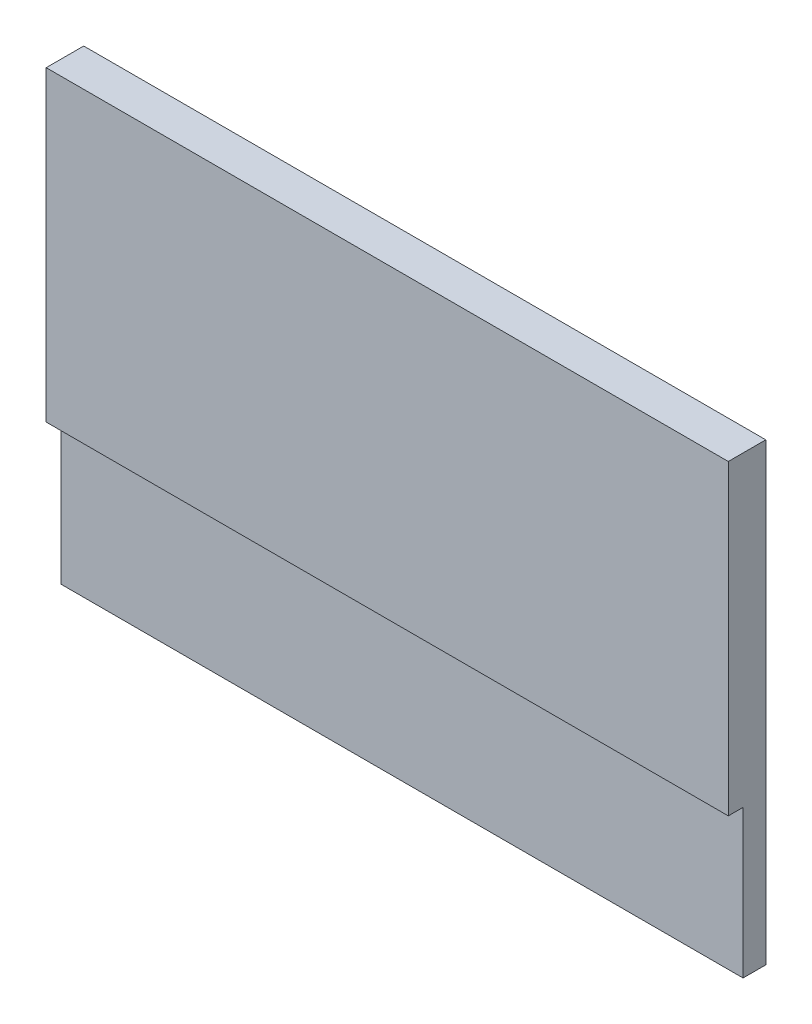
SolidWorks part; units mm, degrees
ref_plane "正面" through (0, 0, 0) normal (0, 0, 1) x (1, 0, 0)
ref_plane "平面" through (0, 0, 0) normal (0, 1, 0) x (1, 0, 0)
ref_plane "右側面" through (0, 0, 0) normal (1, 0, 0) x (0, 0, -1)
sketch "ｽｹｯﾁ1" plane through (0, 0, 0) normal (0, 0, 1) x (1, 0, 0)
  line L1 (0, 0) -> (30, 0)
  line L2 (0, 0) -> (0, 20)
  line L3 (0, 20) -> (30, 20)
  line L4 (30, 0) -> (30, 20)
  dimension "D1" = 30
  dimension "D2" = 20
extrude "ﾎﾞｽ - 押し出し1" add sketch "ｽｹｯﾁ1" along normal blind 1.65
sketch "ｽｹｯﾁ2" plane through (0, 0, 1.65) normal (0, 0, 1) x (1, 0, 0)
  line L0 (30, 0) -> (30, 20) construction
  line L1 (0, 0) -> (30, 0)
  line L2 (0, 0) -> (0, 6.5)
  line L3 (0, 6.5) -> (30, 6.5)
  line L4 (30, 0) -> (30, 6.5)
  line L5 (30, 20) -> (0, 20) construction
  dimension "D1" = 13.5
extrude "ｶｯﾄ - 押し出し1" cut sketch "ｽｹｯﾁ2" against normal blind 0.65
